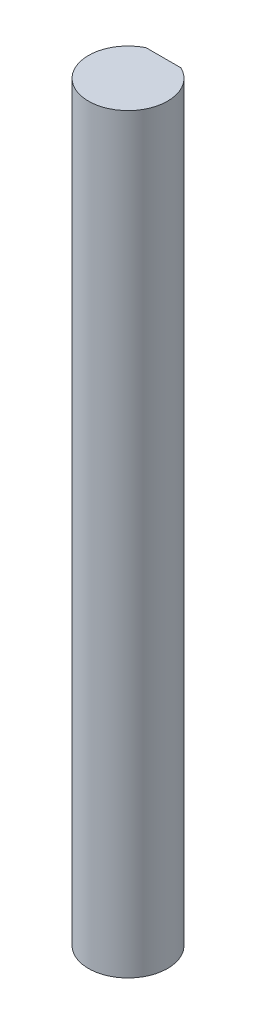
SolidWorks part; units mm, degrees
ref_plane "Front Plane" through (0, 0, 0) normal (0, 0, 1) x (1, 0, 0)
ref_plane "Top Plane" through (0, 0, 0) normal (0, 1, 0) x (1, 0, 0)
ref_plane "Right Plane" through (0, 0, 0) normal (1, 0, 0) x (0, 0, -1)
sketch "Sketch1" plane through (0, 0, 0) normal (0, 1, 0) x (1, 0, 0)
  line L1 (-1.0464, 2.1283) -> (1.0464, 2.1283)
  arc A0 (-1.0464, 2.1283) -> (1.0464, 2.1283) centre (0, 0) ccw
extrude "Boss-Extrude1" add sketch "Sketch1" along normal blind 45
